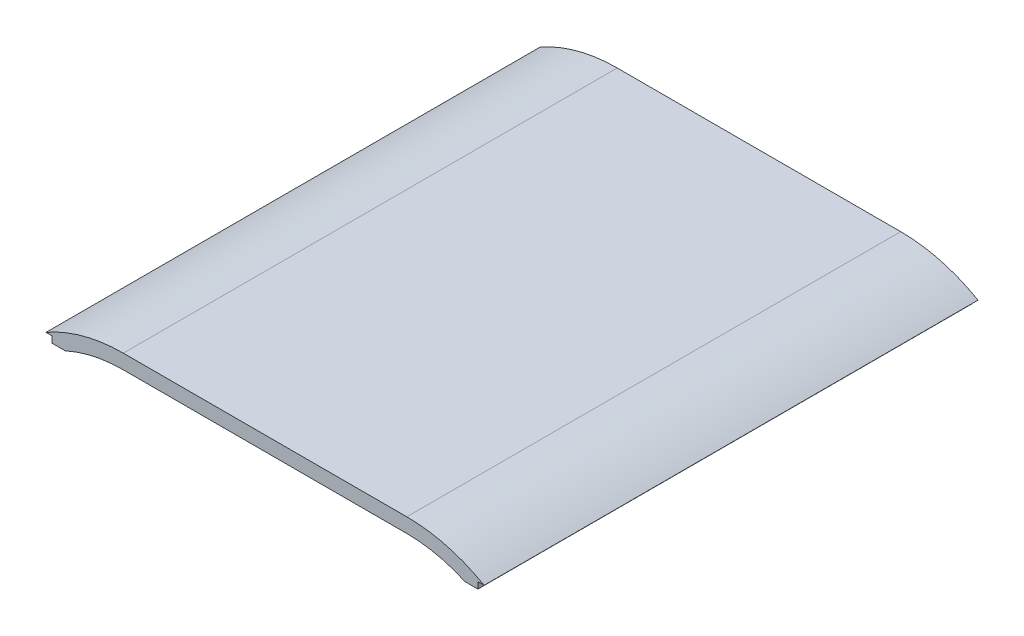
SolidWorks part; units mm, degrees
material "that blue high density foam"
ref_plane "Front" through (0, 0, 0) normal (0, 0, 1) x (1, 0, 0)
ref_plane "Top" through (0, 0, 0) normal (0, 1, 0) x (1, 0, 0)
ref_plane "Right" through (0, 0, 0) normal (1, 0, 0) x (0, 0, -1)
sketch "Sketch1" plane through (0, 0, 0) normal (0, 0, 1) x (1, 0, 0)
  line L1 (-68.5834, 162.2134) -> (68.5834, 162.2134)
  line L2 (-106, 152.2134) -> (-103, 152.2134)
  line L4 (-68.5834, 155.2134) -> (68.5834, 155.2134)
  line L5 (-96.7213, 149.1187) -> (-96.7213, 149.1187)
  line L6 (103, 152.2134) -> (106, 152.2134)
  line L7 (-96.7213, 149.1187) -> (-103, 149.1187)
  line L9 (-103, 149.1187) -> (-103, 152.2134)
  line L13 (0, 169.0467) -> (0, 139.3264) construction
  line L14 (96.7213, 149.1187) -> (103, 149.1187)
  line L15 (103, 149.1187) -> (103, 152.2134)
  arc A0 (-68.5834, 162.2134) -> (-106, 152.2134) centre (-68.5834, 87.2134) ccw construction
  arc A1 (-68.5834, 162.2134) -> (-106, 152.2134) centre (-68.5834, 87.2134) ccw
  arc A2 (106, 152.2134) -> (68.5834, 162.2134) centre (68.5834, 87.2134) ccw construction
  arc A3 (106, 152.2134) -> (68.5834, 162.2134) centre (68.5834, 87.2134) ccw
  arc A5 (-68.5834, 155.2134) -> (-96.7213, 149.1187) centre (-68.5834, 87.2134) ccw
  arc A6 (102.5078, 146.1468) -> (68.5834, 155.2134) centre (68.5834, 87.2134) ccw construction
  arc A7 (68.5834, 155.2134) -> (96.7213, 149.1187) centre (68.5834, 87.2134) cw
  dimension "D1" = 7
extrude "Boss-Extrude1" add sketch "Sketch1" along normal up to surface (239 mm away)
